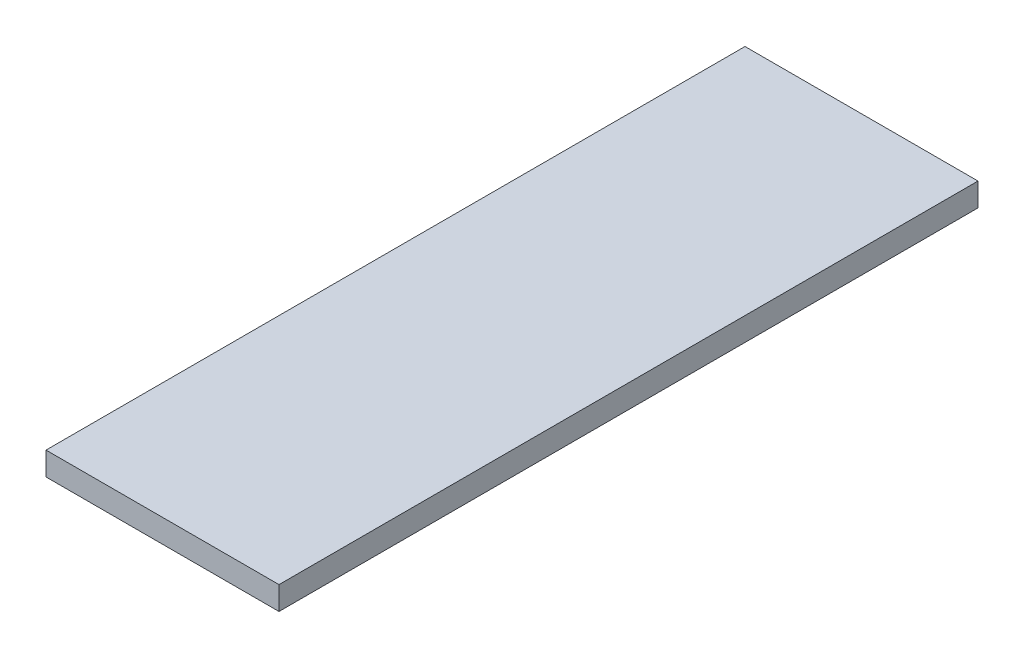
SolidWorks part; units mm, degrees
ref_plane "Plan de face" through (0, 0, 0) normal (0, 0, 1) x (1, 0, 0)
ref_plane "Plan de dessus" through (0, 0, 0) normal (0, 1, 0) x (1, 0, 0)
ref_plane "Plan de droite" through (0, 0, 0) normal (1, 0, 0) x (0, 0, -1)
sketch "Esquisse1" plane through (0, 0, 0) normal (0, 1, 0) x (1, 0, 0)
  line L1 (-6, 18) -> (6, 18)
  line L2 (-6, 18) -> (-6, -18)
  line L3 (-6, -18) -> (6, -18)
  line L4 (6, 18) -> (6, -18)
  point P4 (6, 0)
  point P6 (0, 18)
  dimension "D1" = 36
  dimension "D2" = 12
extrude "Boss.-Extru.1" add sketch "Esquisse1" along normal blind 1.2
